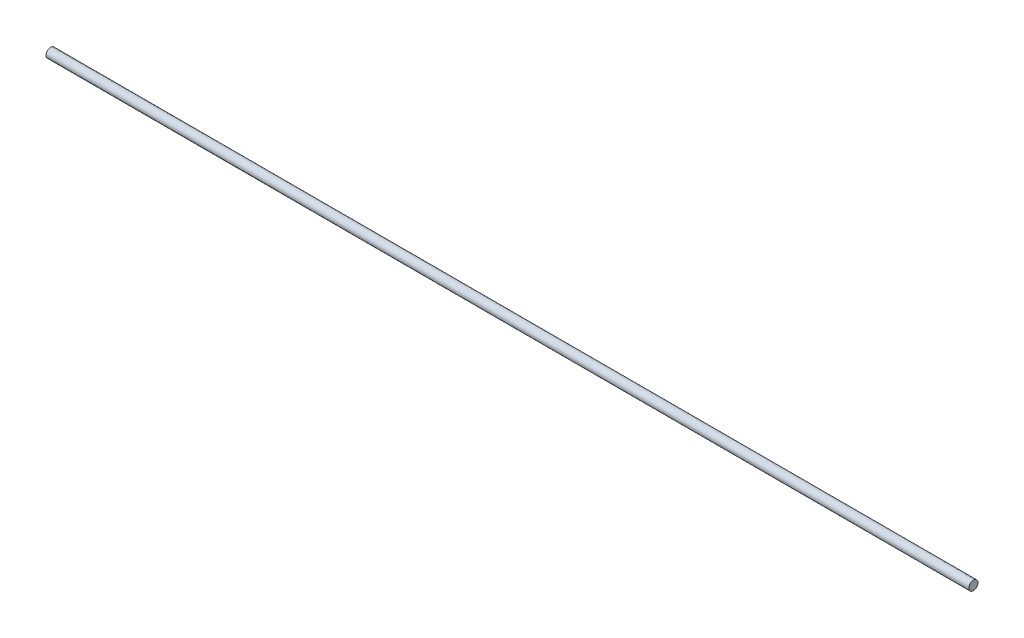
SolidWorks part; units mm, degrees
material "Thornel VCB-20 Carbon Cloth"
ref_plane "Front" through (0, 0, 0) normal (0, 0, 1) x (1, 0, 0)
ref_plane "Top" through (0, 0, 0) normal (0, 1, 0) x (1, 0, 0)
ref_plane "Right" through (0, 0, 0) normal (1, 0, 0) x (0, 0, -1)
sketch "Sketch3" plane through (0, 0, 0) normal (1, 0, 0) x (0, 0, -1)
  circle A0 centre (0, 0) radius 1.5
  dimension "D1" = 3
extrude "Boss-Extrude2" add sketch "Sketch3" along normal blind 300
